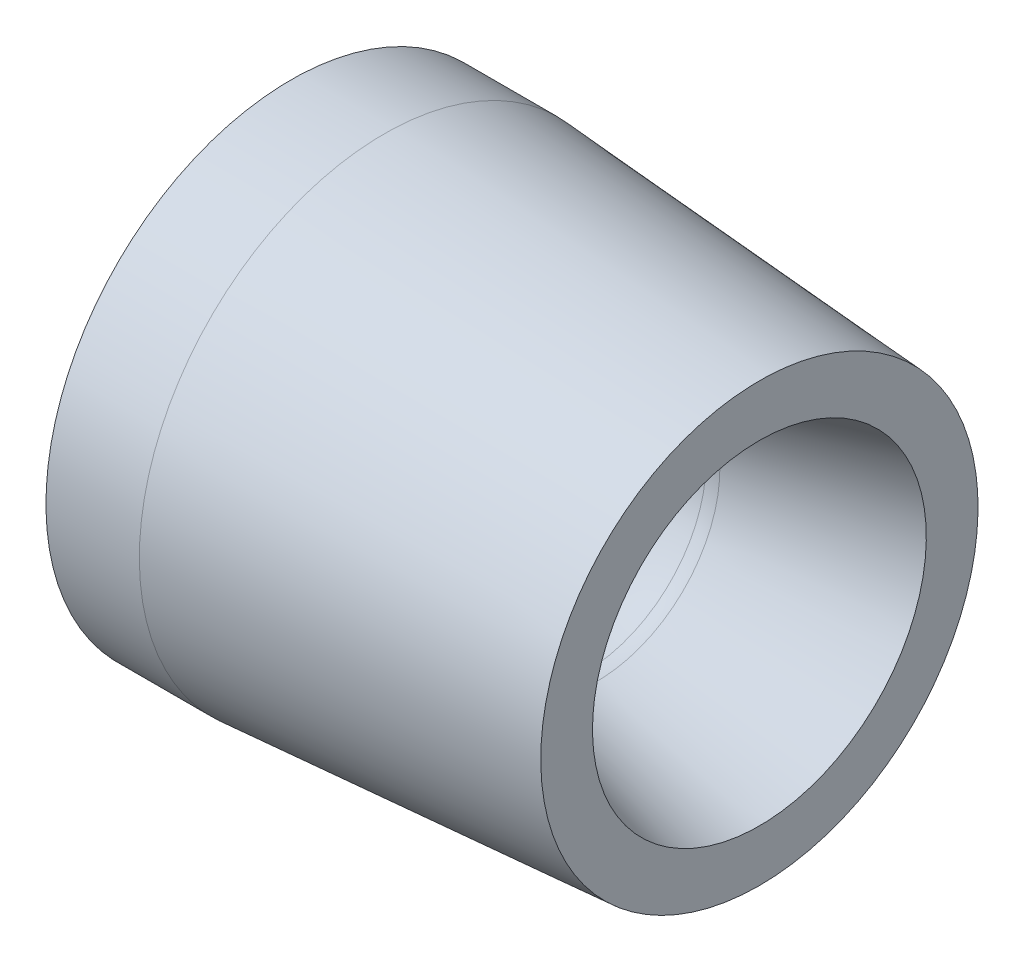
SolidWorks part; units mm, degrees
material "C (Graphite)"
ref_plane "Front Plane" through (0, 0, 0) normal (0, 0, 1) x (1, 0, 0)
ref_plane "Top Plane" through (0, 0, 0) normal (0, 1, 0) x (1, 0, 0)
ref_plane "Right Plane" through (0, 0, 0) normal (1, 0, 0) x (0, 0, -1)
sketch "Sketch1" plane through (0, 0, 0) normal (0, 0, 1) x (1, 0, 0)
  line L0 (0, 0) -> (0, 17.653) construction
  line L1 (0, 17.653) -> (0, 24.511) construction
  line L2 (0, 17.653) -> (0, 44.323) construction
  line L3 (0, 0) -> (90.17, 0) construction
  line L4 (90.17, 0) -> (90.17, 41.656) construction
  line L5 (1.7808, 17.8883) -> (90.17, 41.656)
  line L6 (0, 0) -> (-59.69, 0) construction
  line L7 (-59.69, 0) -> (-59.69, 38.1) construction
  line L8 (-59.69, 38.1) -> (-9.3108, 19.3311)
  line L9 (-59.69, 38.1) -> (90.17, 41.656)
  line L10 (-59.69, 38.1) -> (-59.69, 50.8)
  line L11 (90.17, 41.656) -> (90.17, 50.8)
  line L12 (-59.69, 50.8) -> (90.17, 50.8)
  arc A0 (-9.3108, 19.3311) -> (0, 17.653) centre (0, 44.323) ccw
  arc A1 (0, 17.653) -> (1.7808, 17.8883) centre (0, 24.511) ccw
  dimension "D1" = 17.653
  dimension "D2" = 6.858
  dimension "D3" = 26.67
  dimension "D4" = 90.17
  dimension "D5" = 41.656
  dimension "D6" = 59.69
  dimension "D7" = 38.1
  dimension "D8" = 12.7
revolve "Revolve1" add sketch "Sketch1" angle 360 about L6
sketch "Sketch2" plane through (0, 0, 0) normal (0, 0, 1) x (1, 0, 0)
  line L0 (0, 0) -> (0, 48.3786) construction
  line L1 (0, 31.75) -> (25.4, 31.75)
  line L2 (0, 31.75) -> (-50.8, 31.75)
  line L3 (-50.8, 31.75) -> (-50.8, 0)
  line L4 (-50.8, 0) -> (25.4, 0)
  line L5 (25.4, 31.75) -> (25.4, 0)
  line L6 (0, 0) -> (-80.4085, 0) construction
  line L7 (-59.69, 38.1) -> (-9.3108, 19.3311) construction
  line L8 (-80.4085, 0) -> (94.5158, 0)
  line L9 (-80.4085, 0) -> (-80.4085, 51.7454)
  line L10 (-80.4085, 51.7454) -> (94.5158, 51.7454)
  line L11 (94.5158, 0) -> (94.5158, 51.7454)
  line L12 (-59.69, 38.1) -> (-9.3108, 19.3311)
  line L13 (-42.6455, 31.75) -> (-42.6455, 35.56)
  line L14 (-29.0855, 35.56) -> (25.4, 31.75)
  line L15 (-42.6455, 31.75) -> (-44.8452, 35.56)
  line L16 (-42.6455, 35.56) -> (-44.8452, 35.56)
  line L17 (-42.6455, 35.56) -> (-29.0855, 35.56)
  dimension "D1" = 25.4
  dimension "D2" = 50.8
  dimension "D3" = 31.75
  dimension "D4" = 35.56
  dimension "D5" = 30
  dimension "D6" = 4
revolve "Cut-Revolve1" cut sketch "Sketch2" angle 360 about L4
